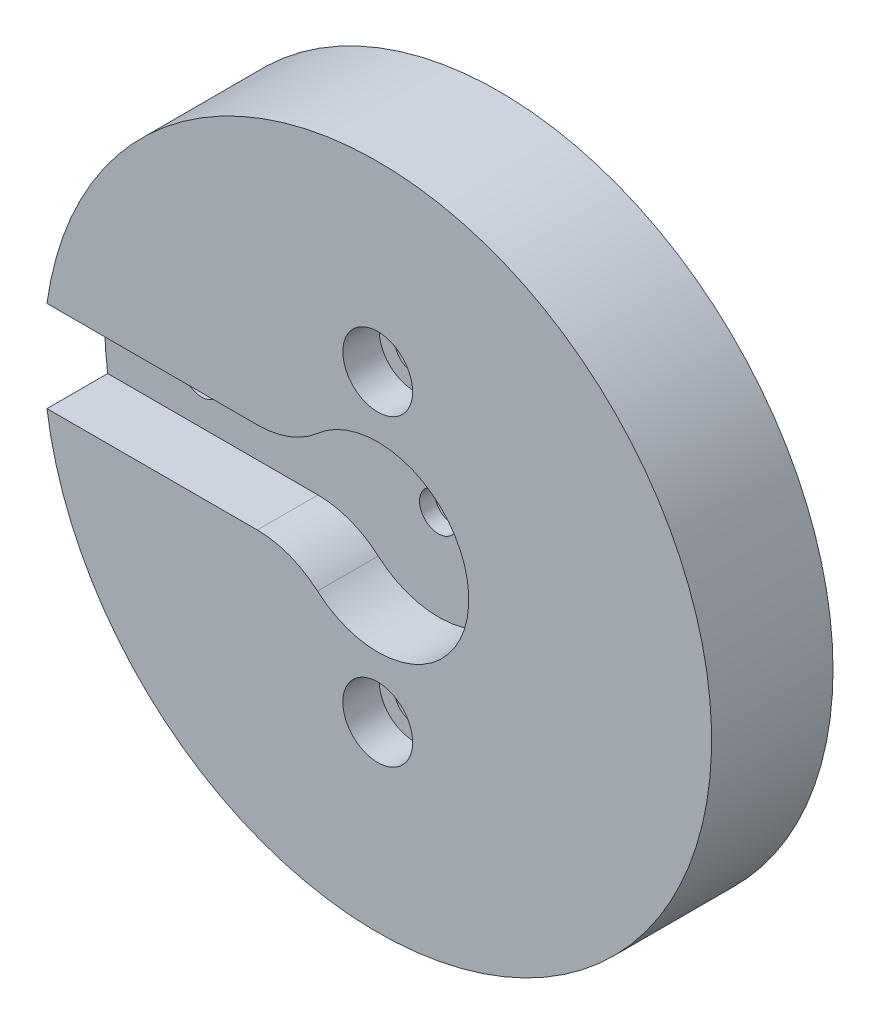
SolidWorks part; units mm, degrees
ref_plane "Front Plane" through (0, 0, 0) normal (0, 0, 1) x (1, 0, 0)
ref_plane "Top Plane" through (0, 0, 0) normal (0, 1, 0) x (1, 0, 0)
ref_plane "Right Plane" through (0, 0, 0) normal (1, 0, 0) x (0, 0, -1)
sketch "Sketch1" plane through (0, 0, 0) normal (0, 0, 1) x (1, 0, 0)
  line L0 (0, 0) -> (0, 6.35) construction
  line L1 (-2.0409, 7.0928) -> (2.0409, 5.6072) construction
  circle A0 centre (0, 0) radius 5.0271 construction
  circle A1 centre (0, 0) radius 7.4083 construction
  circle A2 centre (0, 0) radius 6.35 construction
  circle A3 centre (0, 0) radius 5.967 construction
  circle A4 centre (0, 0) radius 2.3813 construction
  circle A5 centre (0, 0) radius 4.826 construction
  point P8 (304.8, 0)
  point P13 (152.4, 0)
  dimension "OD | Outside Diameter" = 14.8167
  dimension "Root Diameter" = 10.0542
  dimension "Gear Pitch Diameter" = 12.7
  dimension "Base Diameter" = 11.9341
  dimension "For Shaft Diameter" = 4.7625
  dimension "Hub Diameter" = 9.652
  dimension "Pressure Angle" = 20
  dimension "Number of Teeth" = 304.8
  dimension "Gear Pitch | Diametral Pitch" = 609.6
sketch "Sketch2" plane through (0, 0, 0) normal (1, 0, 0) x (0, 0, -1)
  line L0 (-6.35, 0) -> (6.35, 0) construction
  line L1 (-6.35, 7.4083) -> (6.35, 7.4083) construction
  point P2 (0, 7.4083)
  point P4 (0, 0)
  point P6 (0, 7.4083)
  dimension "Overall Width" = 12.7
  dimension "Hub Width" = 6.35
  dimension "Face Width" = 6.35
sketch "Sketch3" plane through (0, 0, 0) normal (0, 0, 1) x (1, 0, 0)
  circle A0 centre (0, 0) radius 7.4083
  circle A1 centre (0, 0) radius 7.4083 construction
extrude "Boss-Extrude1" add sketch "Sketch3" against normal blind 7.62
sketch "Sketch4" plane through (0, 0, 0) normal (0, 0, 1) x (1, 0, 0)
  line L0 (0, 0) -> (4.9933, 0.5818) construction
  line L2 (0, 0) -> (4.9933, -0.5818) construction
  line L4 (4.9933, 0.5818) -> (5.927, 0.6906)
  line L5 (5.927, -0.6906) -> (4.9933, -0.5818)
  arc A0 (4.9933, 0.5818) -> (4.9933, -0.5818) centre (0, 0) cw
  arc A3 (7.2339, 1.5983) -> (7.2339, -1.5983) centre (0, 0) cw
  circle A4 centre (0, 0) radius 7.4083 construction
  spline S0 degree 4 poles (5.927, 0.6906) (5.9293, 0.6909) (5.9359, 0.6919) (5.9484, 0.6942) (5.9686, 0.6987) (5.9942, 0.7052) (6.0271, 0.7148) (6.0655, 0.7275) (6.1073, 0.7428) (6.1523, 0.761) (6.1969, 0.7804) (6.2409, 0.8011) (6.2844, 0.8228) (6.3367, 0.8503) (6.3986, 0.8852) (6.47, 0.9285) (6.5497, 0.9807) (6.6294, 1.0371) (6.7066, 1.0952) (6.7832, 1.1568) (6.8562, 1.2185) (6.9304, 1.2856) (6.9981, 1.3489) (7.0721, 1.4232) (7.1312, 1.484) (7.2071, 1.5675) (7.2513, 1.6179) (7.3023, 1.6779) (7.3245, 1.7051) (7.3382, 1.7219) knots 0 0 0 0 0 0.005377 0.015084 0.028532 0.04661 0.064855 0.092111 0.119476 0.146842 0.174209 0.201575 0.228941 0.256307 0.307035 0.361767 0.4165 0.471232 0.525964 0.580697 0.635429 0.690161 0.744894 0.799626 0.854358 0.909091 0.954545 1 1 1 1 1 construction
  spline S1 degree 4 poles (5.927, 0.6906) (5.9293, 0.6909) (5.9359, 0.6919) (5.9484, 0.6942) (5.9686, 0.6987) (5.9942, 0.7052) (6.0271, 0.7148) (6.0655, 0.7275) (6.1073, 0.7428) (6.1523, 0.761) (6.1969, 0.7804) (6.2409, 0.8011) (6.2844, 0.8228) (6.3367, 0.8503) (6.3986, 0.8852) (6.47, 0.9285) (6.5497, 0.9807) (6.6294, 1.0371) (6.7066, 1.0952) (6.7832, 1.1568) (6.8562, 1.2185) (6.9304, 1.2856) (6.9981, 1.3489) (7.0721, 1.4232) (7.1312, 1.484) (7.1906, 1.5494) (7.2193, 1.5816) (7.2339, 1.5983) knots 0 0 0 0 0 0.005377 0.015084 0.028532 0.04661 0.064855 0.092111 0.119476 0.146842 0.174209 0.201575 0.228941 0.256307 0.307035 0.361767 0.4165 0.471232 0.525964 0.580697 0.635429 0.690161 0.744894 0.799626 0.854358 0.909091 0.909091 0.909091 0.909091 0.909091
  spline S2 degree 4 poles (5.927, -0.6906) (5.9293, -0.6909) (5.9359, -0.6919) (5.9484, -0.6942) (5.9686, -0.6987) (5.9942, -0.7052) (6.0271, -0.7148) (6.0655, -0.7275) (6.1073, -0.7428) (6.1523, -0.761) (6.1969, -0.7804) (6.2409, -0.8011) (6.2844, -0.8228) (6.3367, -0.8503) (6.3986, -0.8852) (6.47, -0.9285) (6.5497, -0.9807) (6.6294, -1.0371) (6.7066, -1.0952) (6.7832, -1.1568) (6.8562, -1.2185) (6.9304, -1.2856) (6.9981, -1.3489) (7.0721, -1.4232) (7.1312, -1.484) (7.2071, -1.5675) (7.2513, -1.6179) (7.3023, -1.6779) (7.3245, -1.7051) (7.3382, -1.7219) knots 0 0 0 0 0 0.005377 0.015084 0.028532 0.04661 0.064855 0.092111 0.119476 0.146842 0.174209 0.201575 0.228941 0.256307 0.307035 0.361767 0.4165 0.471232 0.525964 0.580697 0.635429 0.690161 0.744894 0.799626 0.854358 0.909091 0.954545 1 1 1 1 1 construction
  spline S3 degree 4 poles (5.927, -0.6906) (5.9293, -0.6909) (5.9359, -0.6919) (5.9484, -0.6942) (5.9686, -0.6987) (5.9942, -0.7052) (6.0271, -0.7148) (6.0655, -0.7275) (6.1073, -0.7428) (6.1523, -0.761) (6.1969, -0.7804) (6.2409, -0.8011) (6.2844, -0.8228) (6.3367, -0.8503) (6.3986, -0.8852) (6.47, -0.9285) (6.5497, -0.9807) (6.6294, -1.0371) (6.7066, -1.0952) (6.7832, -1.1568) (6.8562, -1.2185) (6.9304, -1.2856) (6.9981, -1.3489) (7.0721, -1.4232) (7.1312, -1.484) (7.1906, -1.5494) (7.2193, -1.5816) (7.2339, -1.5983) knots 0 0 0 0 0 0.005377 0.015084 0.028532 0.04661 0.064855 0.092111 0.119476 0.146842 0.174209 0.201575 0.228941 0.256307 0.307035 0.361767 0.4165 0.471232 0.525964 0.580697 0.635429 0.690161 0.744894 0.799626 0.854358 0.909091 0.909091 0.909091 0.909091 0.909091
  dimension "D1" = 10.0542
extrude "Cut-Extrude1" cut sketch "Sketch4" against normal through all both and the other way through all
fillet "Fillet1" radius 0.3551 2 edges at (4.9933, -0.5818, -3.81) (4.9933, 0.5818, -3.81)
pattern_circular "CirPattern1" count 12 over 360 about axis through (0, 0, 6.35) along (0, 0, -1) of "Cut-Extrude1", "Fillet1"
scale "Scale1" bodies to scale 106 scale about origin uniform scaling yes scale factor 2.5
sketch "Sketch10" plane through (0, 0, 0) normal (0, 0, 1) x (1, 0, 0)
  circle A0 centre (0, 0) radius 27.94
  dimension "D1" = 55.88
extrude "Boss-Extrude4" add sketch "Sketch10" along normal blind 10.16
sketch "Sketch11" plane through (0, 0, -19.05) normal (0, 0, -1) x (-1, 0, 0)
  circle A0 centre (0, 0) radius 5.08
  dimension "D1" = 10.16
extrude "Cut-Extrude5" cut sketch "Sketch11" against normal through all
sketch "Sketch12" plane through (0, 0, 10.16) normal (0, 0, 1) x (1, 0, 0)
  line L1 (-10.0803, -3.81) -> (-28.4386, -3.81)
  line L3 (-10.0803, 3.81) -> (-28.4386, 3.81)
  line L4 (-28.4386, -3.81) -> (-28.4386, 3.81)
  arc A0 (-5.0402, -5.715) -> (-5.0402, 5.715) centre (0, 0) ccw
  arc A1 (-10.0803, -3.81) -> (-5.0402, -5.715) centre (-10.0803, -11.43) cw
  arc A2 (-10.0803, 3.81) -> (-5.0402, 5.715) centre (-10.0803, 11.43) ccw
  point P10 (-28.4386, 0)
  dimension "D1" = 7.62
  dimension "D2" = 7.62
  dimension "D3" = 7.62
extrude "Cut-Extrude6" cut sketch "Sketch12" against normal blind 5.08
sketch "Sketch13" plane through (0, 0, 5.08) normal (0, 0, 1) x (1, 0, 0)
  line L0 (0, 0) -> (0, 18.2969) construction
  circle A0 centre (-19.812, 0) radius 1.5875
  dimension "D1" = 3.175
  dimension "D2" = 19.812
extrude "Cut-Extrude12" cut sketch "Sketch13" against normal through all
sketch "Sketch16" plane through (0, 0, 0) normal (0, 0, -1) x (-1, 0, 0)
  circle A0 centre (19.812, 0) radius 2.7496
  dimension "D1" = 5.4991
extrude "Cut-Extrude13" cut sketch "Sketch16" against normal blind 3.81
sketch "Sketch17" plane through (0, 0, -19.05) normal (0, 0, -1) x (-1, 0, 0)
  circle A0 centre (0, 0) radius 12.7
  dimension "D1" = 25.4
sketch "Sketch18" plane through (0, 0, -19.05) normal (0, 0, -1) x (-1, 0, 0)
  circle A0 centre (0, 0) radius 5.08
extrude "Boss-Extrude5" add sketch "Sketch18" against normal up to surface (24.13 mm away) up to face at (-18.2245, 0, 5.08)
sketch "Sketch19" plane through (0, 0, -19.05) normal (0, 0, -1) x (-1, 0, 0)
  circle A0 centre (0, 0) radius 2.794
  dimension "D1" = 5.588
extrude "Cut-Extrude14" cut sketch "Sketch19" against normal blind 22.86
sketch "Sketch20" plane through (0, 0, 3.81) normal (0, 0, -1) x (-1, 0, 0)
  circle A0 centre (0, 0) radius 1.5875
  dimension "D1" = 3.175
extrude "Cut-Extrude15" cut sketch "Sketch20" against normal blind 7.62
sketch "Sketch21" plane through (0, 0, -19.05) normal (0, 0, -1) x (-1, 0, 0)
  circle A0 centre (0, 0) radius 26.2021
extrude "Gear Cut Extrude" cut sketch "Sketch21" against normal up to surface (19.05 mm away) up to face at (-22.5616, 0, 0)
sketch "Sketch22" plane through (0, 0, 10.16) normal (0, 0, 1) x (1, 0, 0)
  line L0 (0, 0) -> (-5.6584, 0) construction
  circle A0 centre (0, 12.7) radius 1.651
  circle A1 centre (0, -12.7) radius 1.651
  dimension "D3" = 3.302
  dimension "D4" = 3.302
  dimension "D1" = 25.4
  dimension "D2" = 12.7
extrude "Cut-Extrude17" cut sketch "Sketch22" against normal up to surface (10.16 mm away) up to face at (27.94, 0, 0)
sketch "Sketch23" plane through (0, 0, 10.16) normal (0, 0, 1) x (1, 0, 0)
  circle A1 centre (0, -12.7) radius 2.921
  circle A2 centre (0, 12.7) radius 2.921
  dimension "D1" = 5.842
  dimension "D2" = 5.842
extrude "Cut-Extrude18" cut sketch "Sketch23" against normal blind 3.048
equation "\"Root Diameter@Sketch1\"=\"Root Diameter\""
equation "\"OD | Outside Diameter@Sketch1\"=\"Outside Diameter\""
equation "\"D1@CirPattern1\"=\"Number of Teeth\""
equation "\"Diametral Pitch\"= 24"
equation "\"Number of Teeth\"= 12"
equation "\"Pressure Angle\"=20"
equation "\"Pitch Diameter\"= \"Number of Teeth\" / \"Diametral Pitch\""
equation "\"Base Diameter\"= \"Pitch Diameter\" * cos ( \"Pressure Angle\" )"
equation "\"Outside Diameter\"= ( \"Number of Teeth\" + 2 ) / \"Diametral Pitch\""
equation "\"Dedendum\"= 1.25 / \"Diametral Pitch\""
equation "\"Root Diameter\"= \"Pitch Diameter\" - ( 2 * \"Dedendum\" )"
equation "\"Pitch Angle\"= 360deg / \"Number of Teeth\""
equation "\"Alpha\"= sqr ( \"Pitch Diameter\" ^ 2 - \"Base Diameter\" ^ 2 ) / \"Base Diameter\" * 180 / PI - \"Pressure Angle\""
equation "\"Beta\"= ( \"Pitch Angle\" / 4 - \"Alpha\" )"
equation "\"Phi\"= sqr ( ( \"Outside Diameter\" / 2 ) ^ 2 - ( \"Base Diameter\" / 2 ) ^ 2 ) / ( \"Base Diameter\" / 2 )"
equation "\"Addendum\"= 1 / \"Diametral Pitch\""
equation "\"WorkingDepth\"= 2 / \"Diametral Pitch\""
equation "\"WholeDepth\"= 2.25 / \"Diametral Pitch\""
equation "\"Clearance\"= 0.25 / \"Diametral Pitch\""
equation "\"ToothThickness\"= ( pi * 2 ) / \"Diametral Pitch\""
equation "\"CircularPitch\"= pi / \"Diametral Pitch\""
equation "\"Number of Teeth@Sketch1\"=\"Number of Teeth\""
equation "\"Gear Pitch | Diametral Pitch@Sketch1\"=\"Diametral Pitch\""
equation "\"Pressure Angle@Sketch1\"=\"Pressure Angle\""
equation "\"Gear Pitch Diameter@Sketch1\"=\"Pitch Diameter\""
equation "\"Base Diameter@Sketch1\"=\"Base Diameter\""
equation "\"Fillet\"= \"Clearance\" * cos ( \"Pressure Angle\" ) * tan ( ( 90 + \"Pressure Angle\" ) / 2 )"
equation "\"D1@Fillet1\"=\"Fillet\""
equation "\"D1@Sketch4\"=if( \"Base Diameter\">\"Root Diameter\",\"Root Diameter\",\"Base Diameter\"-.00001)"
equation "\"D1@Fillet2\"=\"Fillet\""
